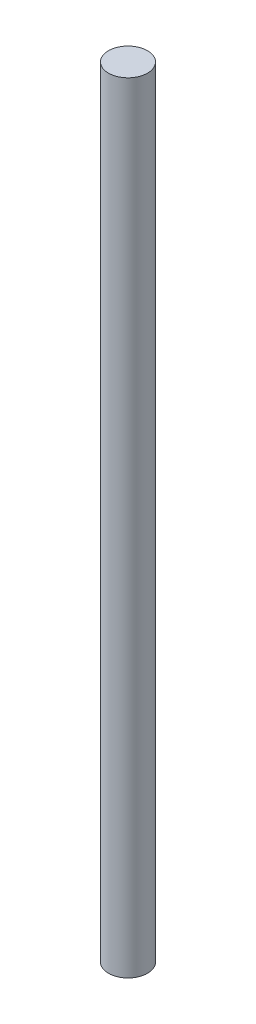
SolidWorks part; units mm, degrees
ref_plane "Front Plane" through (0, 0, 0) normal (0, 0, 1) x (1, 0, 0)
ref_plane "Top Plane" through (0, 0, 0) normal (0, 1, 0) x (1, 0, 0)
ref_plane "Right Plane" through (0, 0, 0) normal (1, 0, 0) x (0, 0, -1)
sketch "Sketch1" plane through (0, 0, 0) normal (0, 1, 0) x (1, 0, 0)
  circle A0 centre (0, 0) radius 3.175
  dimension "D1" = 6.35
extrude "Boss-Extrude1" add sketch "Sketch1" along normal mid plane 127
